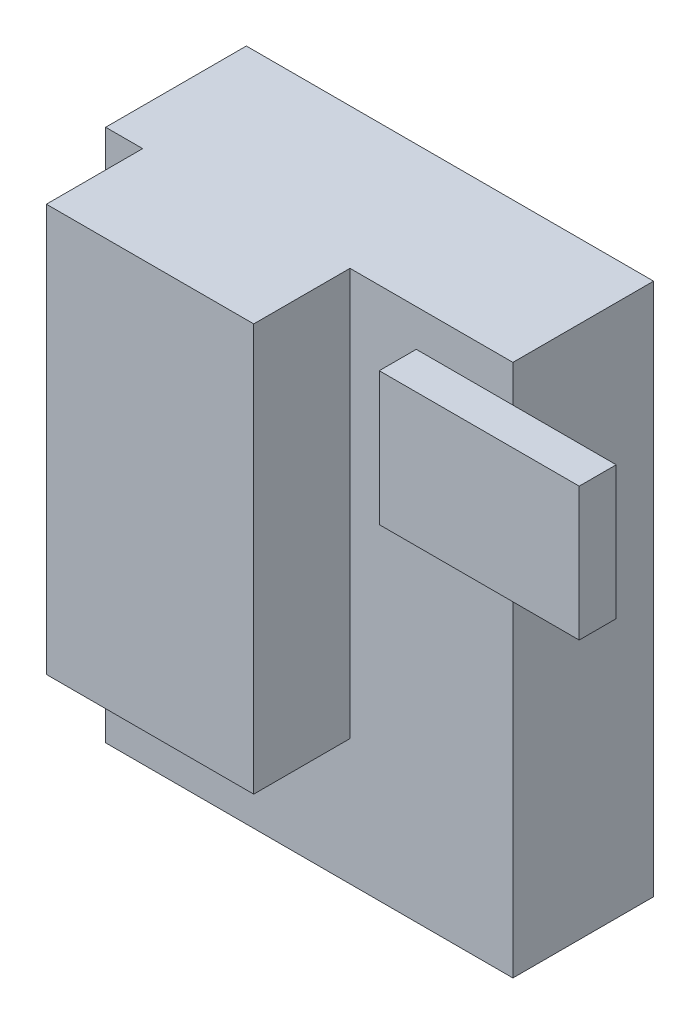
SolidWorks part; units mm, degrees
ref_plane "Ebene vorne" through (0, 0, 0) normal (0, 0, 1) x (1, 0, 0)
ref_plane "Ebene oben" through (0, 0, 0) normal (0, 1, 0) x (1, 0, 0)
ref_plane "Ebene rechts" through (0, 0, 0) normal (1, 0, 0) x (0, 0, -1)
sketch "Skizze1" plane through (0, 0, 0) normal (0, 0, 1) x (1, 0, 0)
  line L1 (-27.2452, 20.289) -> (27.7548, 20.289)
  line L2 (-27.2452, 20.289) -> (-27.2452, -51.711)
  line L3 (-27.2452, -51.711) -> (27.7548, -51.711)
  line L4 (27.7548, 20.289) -> (27.7548, -51.711)
  dimension "D1" = 55
  dimension "D2" = 72
extrude "Aufsatz-Linear austragen1" add sketch "Skizze1" along normal blind 19
sketch "Skizze2" plane through (0, 0, 19) normal (0, 0, 1) x (1, 0, 0)
  line L0 (-27.2452, 20.289) -> (-27.2452, -51.711) construction
  line L1 (-22.2452, 20.289) -> (5.7548, 20.289)
  line L2 (-22.2452, 20.289) -> (-22.2452, -34.711)
  line L3 (-22.2452, -34.711) -> (5.7548, -34.711)
  line L4 (5.7548, 20.289) -> (5.7548, -34.711)
  line L5 (27.7548, 20.289) -> (-27.2452, 20.289) construction
  dimension "D1" = 28
  dimension "D2" = 55
  dimension "D3" = 5
  dimension "D4" = 0
extrude "Aufsatz-Linear austragen2" add sketch "Skizze2" along normal blind 13
sketch "Skizze3" plane through (0, 0, 19) normal (0, 0, 1) x (1, 0, 0)
  line L0 (27.7548, 20.289) -> (5.7548, 20.289) construction
  line L1 (14.7059, 15.289) -> (41.7059, 15.289)
  line L2 (14.7059, 15.289) -> (14.7059, -2.711)
  line L3 (14.7059, -2.711) -> (41.7059, -2.711)
  line L4 (41.7059, 15.289) -> (41.7059, -2.711)
  dimension "D1" = 27
  dimension "D2" = 18
  dimension "D3" = 5
extrude "Aufsatz-Linear austragen3" add sketch "Skizze3" along normal blind 5 contours L1 L4 L3 L2
